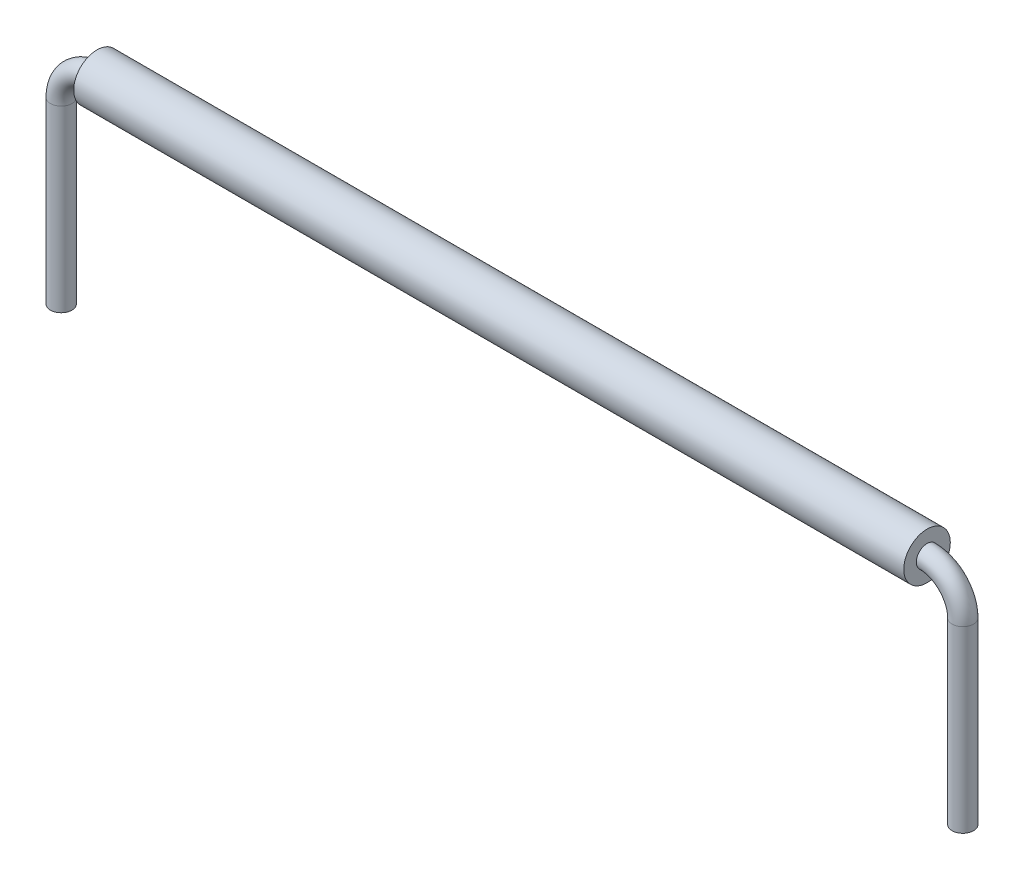
SolidWorks part; units mm, degrees
other "Wire"
other "Insulation"
ref_plane "Front Plane" through (0, 0, 0) normal (0, 0, 1) x (1, 0, 0)
ref_plane "Top Plane" through (0, 0, 0) normal (0, 1, 0) x (1, 0, 0)
ref_plane "Right Plane" through (0, 0, 0) normal (1, 0, 0) x (0, 0, -1)
sketch "Sketch1" plane through (0, 0, 0) normal (0, 0, 1) x (1, 0, 0)
  line L0 (-11.596, 0) -> (11.596, 0)
  line L1 (-12.596, -1) -> (-12.596, -6)
  line L2 (12.596, -1) -> (12.596, -6)
  line L3 (0, 0) -> (0, -6) construction
  line L4 (-12.596, -6) -> (12.596, -6) construction
  arc A0 (-11.596, 0) -> (-12.596, -1) centre (-11.596, -1) ccw
  arc A1 (11.596, 0) -> (12.596, -1) centre (11.596, -1) cw
  dimension "D1" = 1
  dimension "D2" = 25.192
  dimension "D3" = 6
sketch "Sketch2" plane through (0, 0, 0) normal (1, 0, 0) x (0, 0, -1)
  circle A0 centre (0, 0) radius 0.3
  dimension "D1" = 0.6
sweep "Sweep1" add profiles "Sketch2" path "Sketch1"
sketch "Sketch3" plane through (0, 0, 0) normal (1, 0, 0) x (0, 0, -1)
  circle A0 centre (0, 0) radius 0.65
  circle A1 centre (0, 0) radius 0.3
  dimension "D1" = 1.3
  dimension "D2" = 0.6
extrude "Boss-Extrude1" add sketch "Sketch3" along normal up to vertex (11.596 mm away) and the other way up to vertex (11.596 mm away) separate body up to point (11.596, 0, 0) other way up to point (-11.596, 0, 0)
